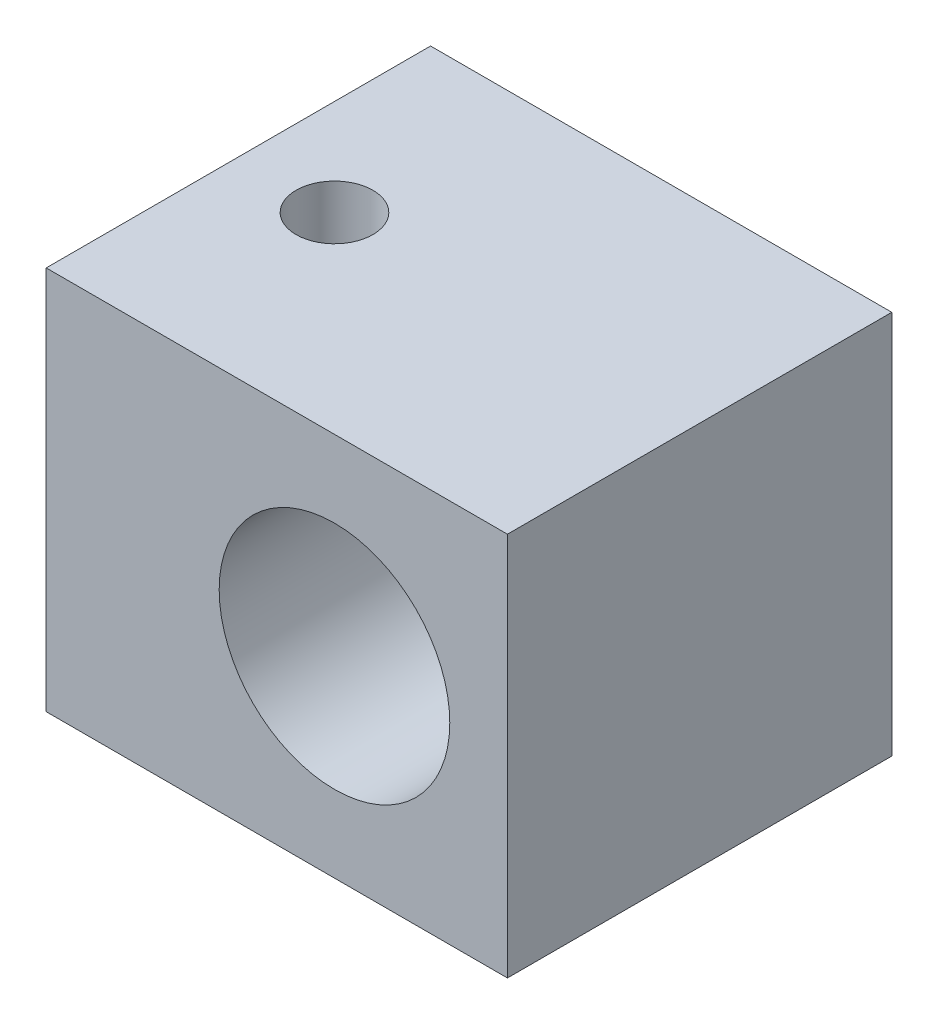
SolidWorks part; units mm, degrees
ref_plane "Plan de face" through (0, 0, 0) normal (0, 0, 1) x (1, 0, 0)
ref_plane "Plan de dessus" through (0, 0, 0) normal (0, 1, 0) x (1, 0, 0)
ref_plane "Plan de droite" through (0, 0, 0) normal (1, 0, 0) x (0, 0, -1)
sketch "Esquisse1" plane through (0, 0, 0) normal (0, 0, 1) x (1, 0, 0)
  line L1 (0, 0) -> (12, 0)
  line L2 (0, 0) -> (0, -10)
  line L3 (0, -10) -> (12, -10)
  line L4 (12, 0) -> (12, -10)
  dimension "D1" = 10
  dimension "D2" = 12
extrude "Boss.-Extru.1" add sketch "Esquisse1" along normal blind 10
sketch "Esquisse2" plane through (0, 0, 0) normal (0, 0, 1) x (1, 0, 0)
  line L0 (12, -10) -> (12, 0) construction
  line L1 (12, 0) -> (0, 0) construction
  circle A0 centre (7.5, -5) radius 3
  dimension "D1" = 6
  dimension "D2" = 4.5
  dimension "D3" = 5
extrude "Enlèv. mat.-Extru.2" cut sketch "Esquisse2" along normal through all
sketch "Esquisse3" plane through (0, 0, 0) normal (0, 1, 0) x (1, 0, 0)
  line L0 (0, -10) -> (0, 0) construction
  line L1 (12, 0) -> (0, 0) construction
  circle A0 centre (2.5, -5) radius 1
  dimension "D1" = 2
  dimension "D2" = 2.5
  dimension "D3" = 5
extrude "Enlèv. mat.-Extru.3" cut sketch "Esquisse3" against normal through all
